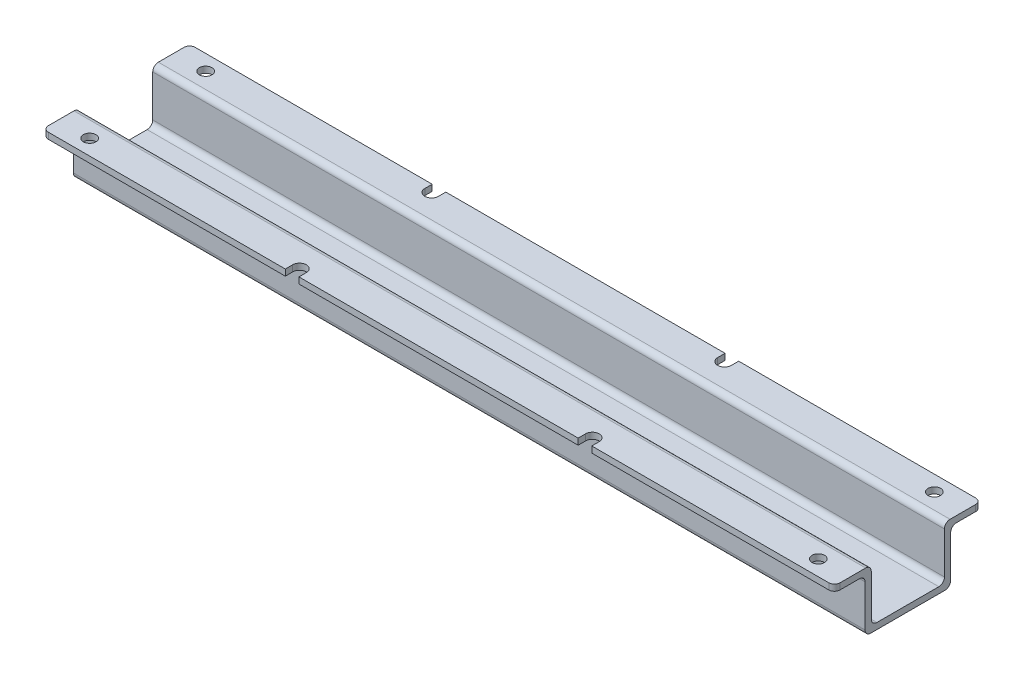
SolidWorks part; units mm, degrees
material "Plain Carbon Steel"
ref_plane "Front Plane" through (0, 0, 0) normal (0, 0, 1) x (1, 0, 0)
ref_plane "Top Plane" through (0, 0, 0) normal (0, 1, 0) x (1, 0, 0)
ref_plane "Right Plane" through (0, 0, 0) normal (1, 0, 0) x (0, 0, -1)
sketch "Sketch1" plane through (0, 0, 0) normal (1, 0, 0) x (0, 0, -1)
  line L0 (0, 0.4934) -> (0, 24.3315) construction
  line L1 (-10.98, 12.11) -> (-10.98, 1.44)
  line L2 (0, 13.3823) -> (0, -13.3823) construction
  line L3 (9.39, 13.7) -> (9.39, 3.03)
  line L4 (-10.83, 15.14) -> (-18.85, 15.14)
  line L5 (10.83, 15.14) -> (18.85, 15.14)
  line L6 (-7.95, 1.59) -> (7.95, 1.59)
  line L8 (-9.39, 13.7) -> (-9.39, 3.03)
  line L9 (-18.85, 15.14) -> (-18.85, 13.55)
  line L10 (-18.85, 13.55) -> (-12.42, 13.55)
  line L14 (-9.54, 0) -> (9.54, 0)
  line L16 (10.98, 1.44) -> (10.98, 12.11)
  line L17 (12.42, 13.55) -> (18.85, 13.55)
  line L18 (18.85, 13.55) -> (18.85, 15.14)
  arc A0 (-10.83, 15.14) -> (-9.39, 13.7) centre (-10.83, 13.7) cw
  arc A1 (-12.42, 13.55) -> (-10.98, 12.11) centre (-12.42, 12.11) cw
  arc A2 (10.98, 12.11) -> (12.42, 13.55) centre (12.42, 12.11) cw
  arc A3 (9.39, 13.7) -> (10.83, 15.14) centre (10.83, 13.7) cw
  arc A4 (9.54, 0) -> (10.98, 1.44) centre (9.54, 1.44) ccw
  arc A5 (9.39, 3.03) -> (7.95, 1.59) centre (7.95, 3.03) cw
  arc A6 (-10.98, 1.44) -> (-9.54, 0) centre (-9.54, 1.44) ccw
  arc A7 (-7.95, 1.59) -> (-9.39, 3.03) centre (-7.95, 3.03) cw
  point P22 (-9.39, 15.14)
  point P29 (9.39, 15.14)
  dimension "D6" = 15.14
  dimension "D4" = 9.46
  dimension "D9" = 1.44
  dimension "D1" = 1.59
  dimension "D2" = 1.59
  dimension "D3" = 1.59
  dimension "D5" = 1.59
  dimension "D8" = 1.59
extrude "Boss-Extrude2" add sketch "Sketch1" against normal blind 203.2
fillet "Fillet4" radius 1.44 4 edges at (-203.2, 14.345, -18.85) (-203.2, 14.345, 18.85) (0, 14.345, 18.85) (0, 14.345, -18.85)
sketch "Sketch3" plane through (0, 15.14, 0) normal (0, 1, 0) x (1, 0, 0)
  line L0 (-203.2, 0) -> (0, 0) construction
  line L1 (-203.2, 7.95) -> (-203.2, -7.95) construction
  line L2 (-101.6, 18.85) -> (-101.6, -18.85) construction
  line L3 (-201.76, 18.85) -> (-1.44, 18.85) construction
  line L4 (-201.76, -18.85) -> (-1.44, -18.85) construction
  line L5 (-203.2, 17.41) -> (-203.2, 10.83) construction
  line L6 (-137.43, -16.95) -> (-137.43, -18.85)
  line L7 (-137.43, -18.85) -> (-140.93, -18.85)
  line L8 (-140.93, 18.85) -> (-140.93, 16.95)
  line L9 (-140.93, -18.85) -> (-140.93, -16.95)
  line L10 (-137.43, 16.95) -> (-137.43, 18.85)
  line L11 (-137.43, 18.85) -> (-140.93, 18.85)
  line L12 (-65.77, -16.95) -> (-65.77, -18.85)
  line L13 (-62.27, -18.85) -> (-62.27, -16.95)
  line L14 (-65.77, -18.85) -> (-62.27, -18.85)
  line L15 (-65.77, 16.95) -> (-65.77, 18.85)
  line L16 (-65.77, 18.85) -> (-62.27, 18.85)
  line L17 (-62.27, 18.85) -> (-62.27, 16.95)
  circle A0 centre (-101.6, 0) radius 1.61
  circle A1 centre (-26.27, 0) radius 1.735
  circle A2 centre (-176.93, 0) radius 1.735
  circle A3 centre (-195.11, 14.89) radius 1.61
  arc A4 (-140.93, 16.95) -> (-137.43, 16.95) centre (-139.18, 16.95) ccw
  arc A5 (-140.93, -16.95) -> (-137.43, -16.95) centre (-139.18, -16.95) cw
  circle A6 centre (-195.11, -14.89) radius 1.61
  arc A7 (-62.27, -16.95) -> (-65.77, -16.95) centre (-64.02, -16.95) ccw
  arc A8 (-62.27, 16.95) -> (-65.77, 16.95) centre (-64.02, 16.95) cw
  circle A9 centre (-8.09, 14.89) radius 1.61
  circle A10 centre (-8.09, -14.89) radius 1.61
  dimension "D1" = 75.33
  dimension "D3" = 3.47
  dimension "D4" = 3.47
  dimension "D5" = 3.22
  dimension "D8" = 8.09
  dimension "D6" = 3.22
  dimension "D12" = 1.75
  dimension "D2" = 75.33
  dimension "D7" = 3.96
  dimension "D9" = 1.9
  dimension "D10" = 1.9
  dimension "D11" = 3.5
extrude "Cut-Extrude2" cut sketch "Sketch3" against normal through all both and the other way through all
